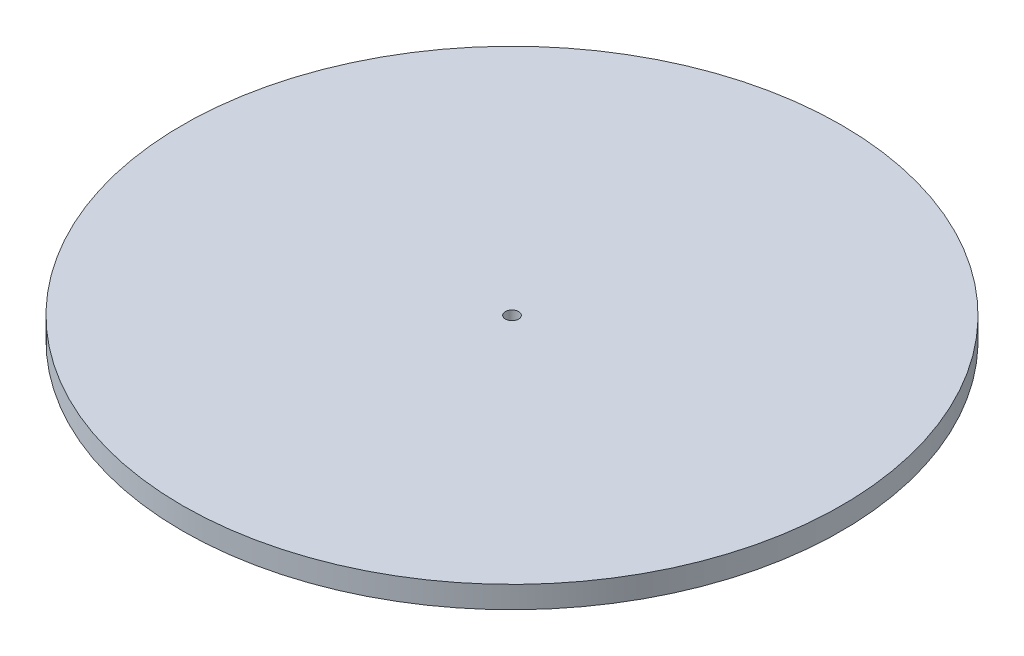
SolidWorks part; units mm, degrees
material "6061-T6 (SS)"
ref_plane "Front Plane" through (0, 0, 0) normal (0, 0, 1) x (1, 0, 0)
ref_plane "Top Plane" through (0, 0, 0) normal (0, 1, 0) x (1, 0, 0)
ref_plane "Right Plane" through (0, 0, 0) normal (1, 0, 0) x (0, 0, -1)
sketch "Sketch1" plane through (0, 0, 0) normal (0, 1, 0) x (1, 0, 0)
  circle A0 centre (0, 0) radius 150
  circle A1 centre (0, 0) radius 3
  dimension "D1" = 300
  dimension "D2" = 6
extrude "Boss-Extrude1" add sketch "Sketch1" along normal blind 10
